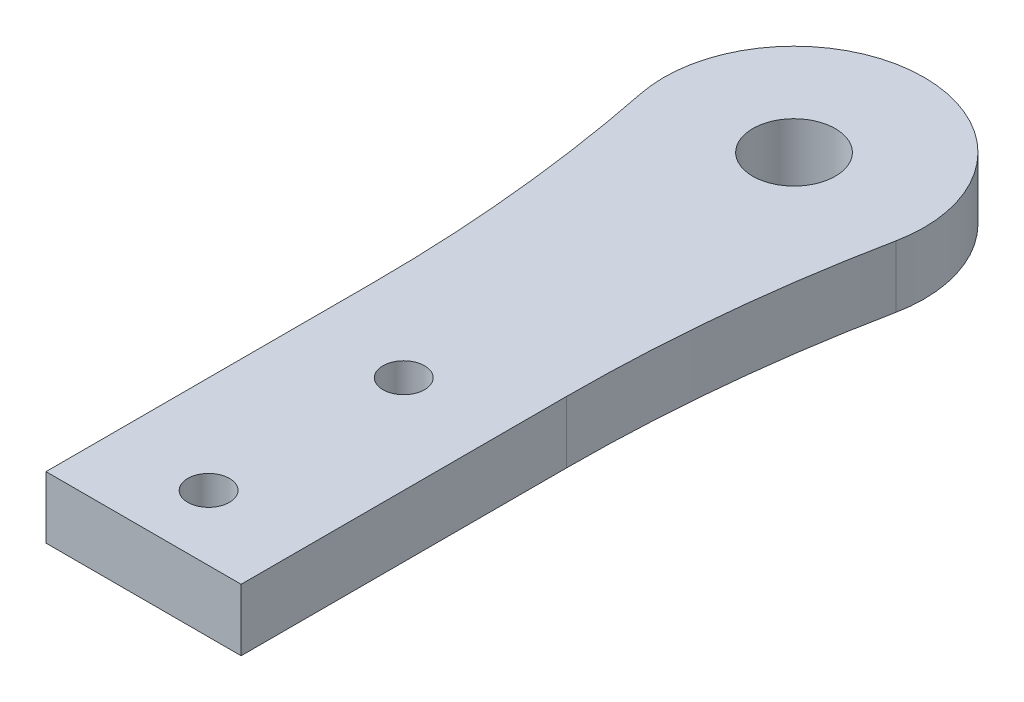
SolidWorks part; units mm, degrees
ref_plane "Front Plane" through (0, 0, 0) normal (0, 0, 1) x (1, 0, 0)
ref_plane "Top Plane" through (0, 0, 0) normal (0, 1, 0) x (1, 0, 0)
ref_plane "Right Plane" through (0, 0, 0) normal (1, 0, 0) x (0, 0, -1)
sketch "Sketch1" plane through (0, 0, 0) normal (0, 1, 0) x (1, 0, 0)
  line L0 (0, 0) -> (0, 50) construction
  line L1 (-7.5, 0) -> (7.5, 0)
  line L2 (7.5, 0) -> (7.5, 25)
  line L3 (-7.5, 25) -> (-7.5, 0)
  arc A0 (7.5, 25) -> (9.802, 48.0198) centre (123.75, 25) cw
  arc A1 (9.802, 48.0198) -> (-9.802, 48.0198) centre (0, 50) ccw
  arc A2 (-9.802, 48.0198) -> (-7.5, 25) centre (-123.75, 25) cw
  circle A3 centre (0, 50) radius 3.175
  circle A4 centre (0, 5) radius 1.6
  circle A5 centre (0, 20) radius 1.6
  dimension "D2" = 10
  dimension "D3" = 6.35
  dimension "D6" = 3.2
  dimension "D1" = 15
  dimension "D4" = 50
  dimension "D5" = 25
  dimension "D7" = 5
  dimension "D8" = 15
extrude "Boss-Extrude1" add sketch "Sketch1" along normal blind 4.7625
